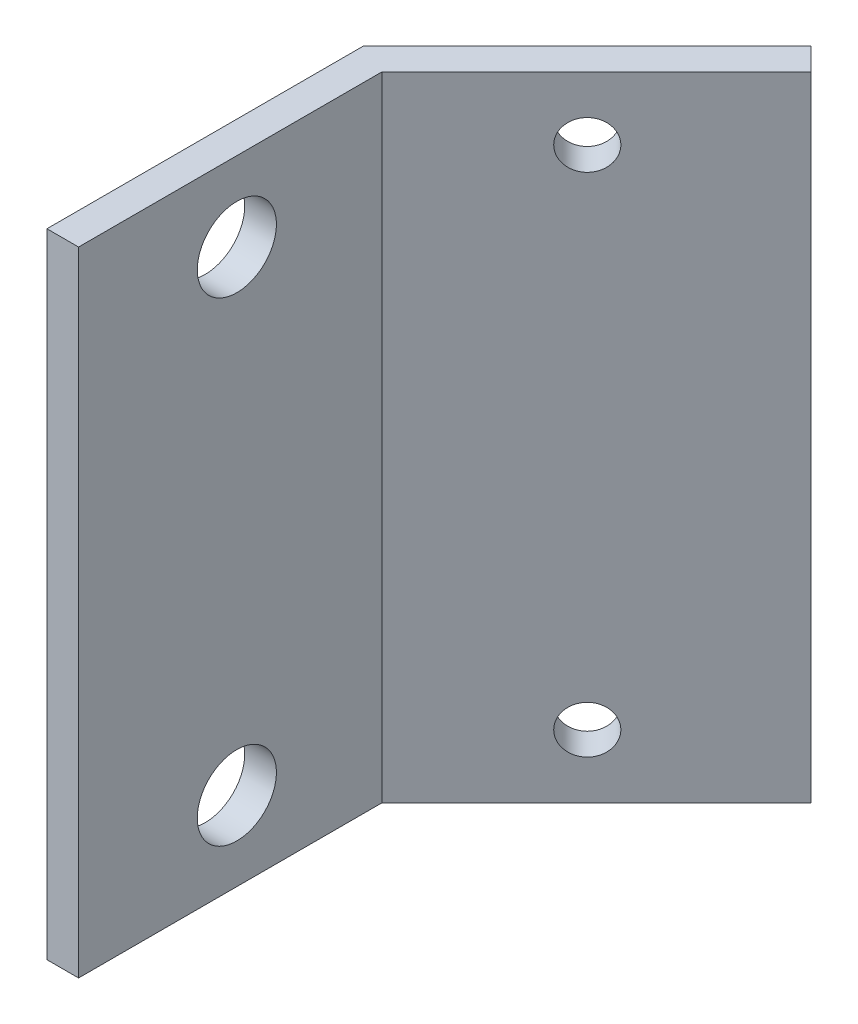
SolidWorks part; units mm, degrees
ref_plane "Plan de face" through (0, 0, 0) normal (0, 0, 1) x (1, 0, 0)
ref_plane "Plan de dessus" through (0, 0, 0) normal (0, 1, 0) x (1, 0, 0)
ref_plane "Plan de droite" through (0, 0, 0) normal (1, 0, 0) x (0, 0, -1)
sketch "Esquisse1" plane through (0, 0, 0) normal (0, 1, 0) x (1, 0, 0)
  line L0 (0, 0) -> (0, 20)
  line L1 (0, 20) -> (14.1421, 34.1421)
  line L2 (14.1421, 34.1421) -> (15.5563, 32.7279)
  line L3 (15.5563, 32.7279) -> (2, 19.1716)
  line L4 (2, 19.1716) -> (2, 0)
  line L5 (2, 0) -> (0, 0)
  dimension "D1" = 2
  dimension "D2" = 20
  dimension "D3" = 45
extrude "Extrusion1" add sketch "Esquisse1" along normal blind 40
sketch "Esquisse3" plane through (0, 0, 0) normal (-1, 0, 0) x (0, 0, 1)
  line L0 (-10, 0) -> (-10, 40) construction
  line L1 (-20, 0) -> (0, 0) construction
  line L2 (-20, 40) -> (0, 40) construction
  line L3 (0, 20) -> (-20, 20) construction
  line L4 (0, 40) -> (0, 0) construction
  line L5 (-20, 40) -> (-20, 0) construction
  line L6 (0, 5) -> (-20, 5) construction
  circle A0 centre (-10, 5) radius 2.5
  circle A1 centre (-10, 35) radius 2.5
  dimension "D1" = 5
  dimension "D2" = 5
extrude "Extrusion2" cut sketch "Esquisse3" against normal up to next
sketch "Esquisse4" plane through (-10, 0, -10) normal (-0.7071, 0, -0.7071) x (-0.7071, 0, 0.7071)
  line L0 (-24.1421, 40) -> (-24.1421, 0) construction
  line L1 (-34.1421, 40) -> (-14.1421, 40) construction
  line L2 (-34.1421, 0) -> (-14.1421, 0) construction
  line L3 (-34.1421, 20) -> (-14.1421, 20) construction
  line L4 (-34.1421, 40) -> (-34.1421, 0) construction
  line L5 (-14.1421, 40) -> (-14.1421, 0) construction
  line L6 (-34.1421, 36) -> (-14.1421, 36) construction
  circle A0 centre (-24.1421, 36) radius 1.5
  circle A1 centre (-24.1421, 4) radius 1.5
  dimension "D2" = 3
  dimension "D1" = 4
extrude "Extrusion3" cut sketch "Esquisse4" against normal up to next
